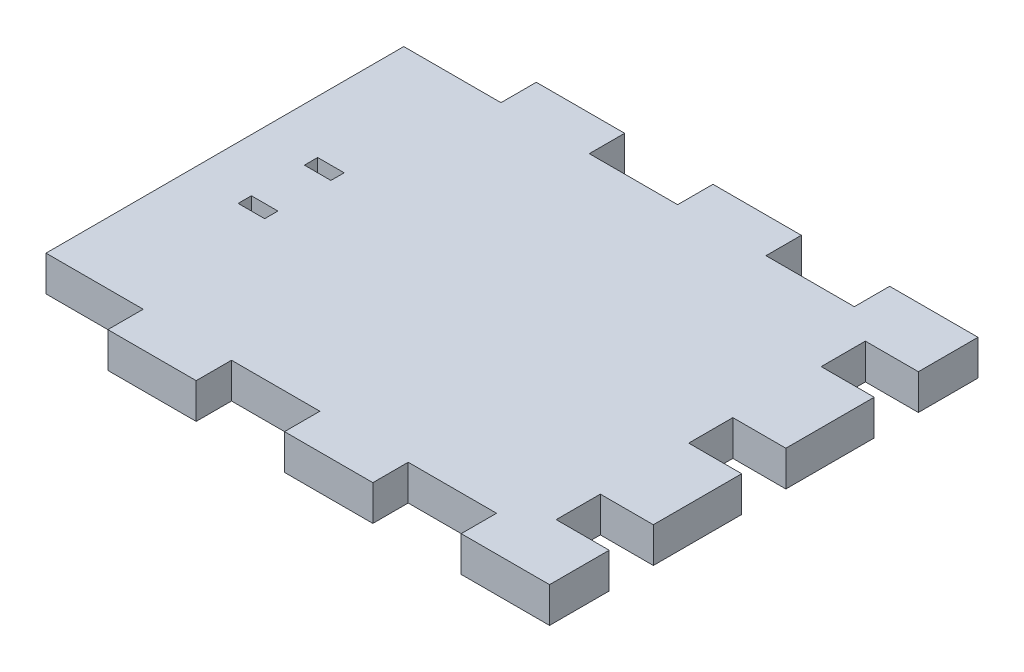
SolidWorks part; units mm, degrees
material "Maple"
ref_plane "Front Plane" through (0, 0, 0) normal (0, 0, 1) x (1, 0, 0)
ref_plane "Top Plane" through (0, 0, 0) normal (0, 1, 0) x (1, 0, 0)
ref_plane "Right Plane" through (0, 0, 0) normal (1, 0, 0) x (0, 0, -1)
sketch "Sketch1" plane through (0, 0, 0) normal (0, 1, 0) x (1, 0, 0)
  line L1 (0, 0) -> (55, 0)
  line L2 (0, 0) -> (0, -40.5)
  line L3 (0, -40.5) -> (55, -40.5)
  line L4 (55, 0) -> (55, -40.5)
  dimension "D1" = 55
  dimension "D2" = 40.5
extrude "Boss-Extrude1" add sketch "Sketch1" along normal blind 4
sketch "Sketch2" plane through (55, 0, 0) normal (1, 0, 0) x (0, 0, -1)
  line L0 (-40.5, 4) -> (-40.5, 0) construction
  line L1 (-40.5, 4) -> (-37.75, 4)
  line L2 (-40.5, 4) -> (-40.5, 0)
  line L3 (-40.5, 0) -> (-37.75, 0)
  line L4 (-37.75, 4) -> (-37.75, 0)
  line L5 (-40.5, 4) -> (0, 4) construction
  line L6 (-40.5, 0) -> (0, 0) construction
  line L7 (0, 4) -> (0, 0) construction
  line L8 (-32.75, 4) -> (-22.75, 4)
  line L9 (-32.75, 4) -> (-32.75, 0)
  line L10 (-32.75, 0) -> (-22.75, 0)
  line L11 (-22.75, 4) -> (-22.75, 0)
  line L12 (-17.75, 4) -> (-7.75, 4)
  line L13 (-17.75, 4) -> (-17.75, 0)
  line L14 (-17.75, 0) -> (-7.75, 0)
  line L15 (-7.75, 4) -> (-7.75, 0)
  line L16 (-2.75, 4) -> (0, 4)
  line L17 (-2.75, 4) -> (-2.75, 0)
  line L18 (-2.75, 0) -> (0, 0)
  line L19 (0, 4) -> (0, 0)
  dimension "D1" = 2.75
  dimension "D2" = 5
  dimension "D3" = 5
  dimension "D4" = 5
  dimension "D5" = 10
  dimension "D6" = 2.75
extrude "Boss-Extrude2" add sketch "Sketch2" along normal blind 6
sketch "Sketch3" plane through (0, 4, 0) normal (0, 1, 0) x (1, 0, 0)
  line L0 (61, 0) -> (0, 0) construction
  line L1 (61, 0) -> (51, 0)
  line L2 (61, 0) -> (61, 4)
  line L3 (61, 4) -> (51, 4)
  line L4 (51, 0) -> (51, 4)
  line L5 (61, -40.5) -> (51, -40.5)
  line L6 (61, -40.5) -> (61, -44.5)
  line L7 (61, -44.5) -> (51, -44.5)
  line L8 (51, -40.5) -> (51, -44.5)
  dimension "D1" = 4
  dimension "D2" = 10
extrude "Boss-Extrude3" add sketch "Sketch3" against normal through all
pattern_linear "LPattern1" count 3 spacing 20 along (-1, 0, 0) of "Boss-Extrude3"
sketch "Sketch4" plane through (0, 4, 0) normal (0, 1, 0) x (1, 0, 0)
  line L0 (0, -20.25) -> (81, -20.25) construction
  line L1 (0, 0) -> (0, -40.5) construction
  line L3 (6, -23.25) -> (9, -23.25)
  line L4 (6, -23.25) -> (6, -24.75)
  line L5 (6, -24.75) -> (9, -24.75)
  line L6 (9, -23.25) -> (9, -24.75)
  line L7 (6, -17.25) -> (9, -17.25)
  line L8 (6, -17.25) -> (6, -15.75)
  line L9 (6, -15.75) -> (9, -15.75)
  line L10 (9, -17.25) -> (9, -15.75)
  dimension "D1" = 3
  dimension "D2" = 1.5
  dimension "D3" = 3
  dimension "D4" = 6
  dimension "D5" = 3
  dimension "D6" = 3
extrude "Cut-Extrude1" cut sketch "Sketch4" against normal through all
equation "\"D5@Sketch4\"=\"D3@Sketch4\""
equation "\"D6@Sketch4\"=\"D1@Sketch4\""
